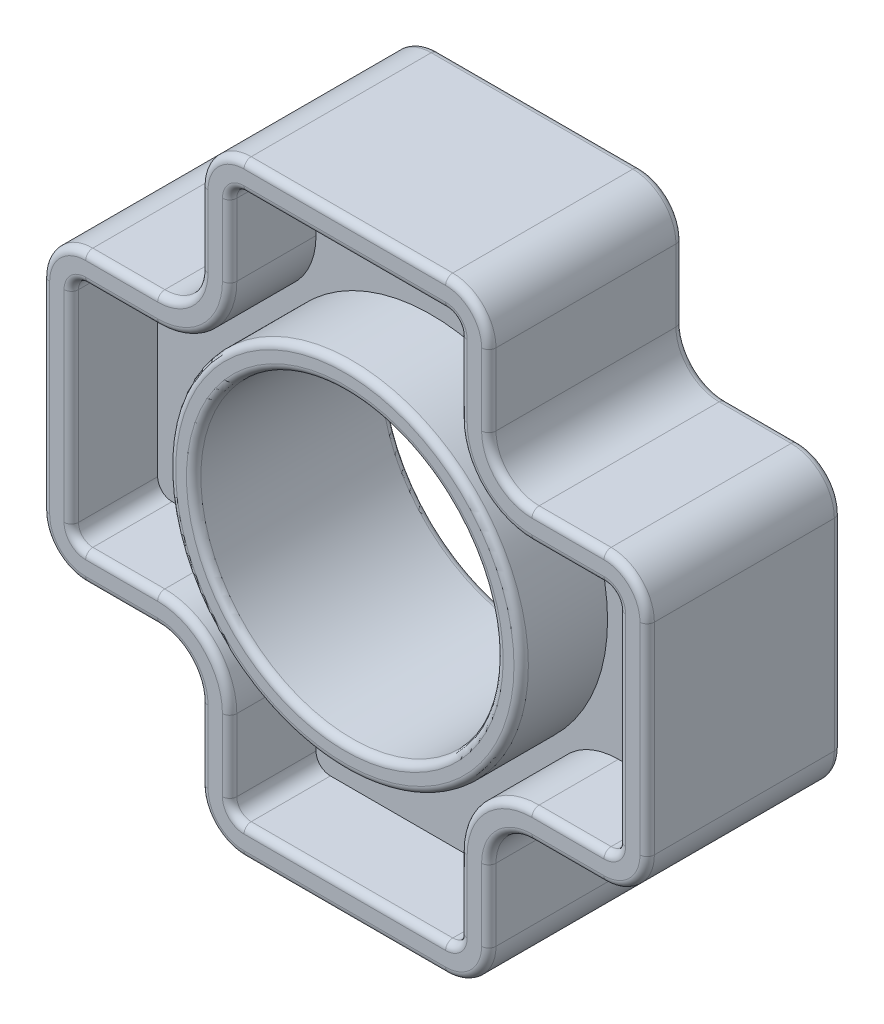
SolidWorks part; units mm, degrees
ref_plane "前基準面" through (0, 0, 0) normal (0, 0, 1) x (1, 0, 0)
ref_plane "上基準面" through (0, 0, 0) normal (0, 1, 0) x (1, 0, 0)
ref_plane "右基準面" through (0, 0, 0) normal (1, 0, 0) x (0, 0, -1)
sketch "草圖1" plane through (0, 0, 0) normal (0, 0, 1) x (1, 0, 0)
  line L0 (-10, 21) -> (-10, 10)
  line L1 (-10, 10) -> (-21, 10)
  line L2 (-21, 10) -> (-21, -10)
  line L3 (-21, -10) -> (-10, -10)
  line L4 (-10, -10) -> (-10, -21)
  line L5 (-10, -21) -> (10, -21)
  line L6 (10, -21) -> (10, -10)
  line L7 (10, -10) -> (21, -10)
  line L8 (21, -10) -> (21, 10)
  line L9 (21, 10) -> (10, 10)
  line L10 (10, 10) -> (10, 21)
  line L11 (10, 21) -> (-10, 21)
  point P2 (0, 21)
  point P13 (-21, 0)
  dimension "D1" = 20
  dimension "D2" = 11
extrude "填料-伸長1" add sketch "草圖1" along normal blind 13.5
fillet "圓角1" radius 3 12 edges at (-10, 10, 6.75) (-21, 10, 6.75) (-10, -10, 6.75) (-21, -10, 6.75) (-10, -21, 6.75) (10, -10, 6.75) (10, -21, 6.75) (21, -10, 6.75) (21, 10, 6.75) (10, 10, 6.75) (10, 21, 6.75) (-10, 21, 6.75)
sketch "草圖2" plane through (0, 0, 13.5) normal (0, 0, 1) x (1, 0, 0)
  line L24 (-13, 8) -> (-18, 8)
  line L25 (-19, 7) -> (-19, -7)
  line L26 (-18, -8) -> (-13, -8)
  line L27 (-8, -13) -> (-8, -18)
  line L28 (-7, -19) -> (7, -19)
  line L29 (8, -18) -> (8, -13)
  line L30 (13, -8) -> (18, -8)
  line L31 (19, -7) -> (19, 7)
  line L32 (18, 8) -> (13, 8)
  line L33 (8, 13) -> (8, 18)
  line L34 (7, 19) -> (-7, 19)
  line L35 (-8, 18) -> (-8, 13)
  line L36 (-13, 8) -> (-18, 8)
  line L37 (-19, 7) -> (-19, -7)
  line L38 (-18, -8) -> (-13, -8)
  line L39 (-8, -13) -> (-8, -18)
  line L40 (-7, -19) -> (7, -19)
  line L41 (8, -18) -> (8, -13)
  line L42 (13, -8) -> (18, -8)
  line L43 (19, -7) -> (19, 7)
  line L44 (18, 8) -> (13, 8)
  line L45 (8, 13) -> (8, 18)
  line L46 (7, 19) -> (-7, 19)
  line L47 (-8, 18) -> (-8, 13)
  arc A24 (-8, -13) -> (-13, -8) centre (-13, -13) ccw
  arc A25 (13, -8) -> (8, -13) centre (13, -13) ccw
  arc A26 (8, 13) -> (13, 8) centre (13, 13) ccw
  arc A27 (-13, 8) -> (-8, 13) centre (-13, 13) ccw
  arc A28 (-8, -13) -> (-13, -8) centre (-13, -13) ccw
  arc A29 (13, -8) -> (8, -13) centre (13, -13) ccw
  arc A30 (8, 13) -> (13, 8) centre (13, 13) ccw
  arc A31 (-13, 8) -> (-8, 13) centre (-13, 13) ccw
  arc A32 (-18, 8) -> (-19, 7) centre (-18, 7) ccw
  arc A33 (-18, 8) -> (-19, 7) centre (-18, 7) ccw
  arc A34 (-19, -7) -> (-18, -8) centre (-18, -7) ccw
  arc A35 (-19, -7) -> (-18, -8) centre (-18, -7) ccw
  arc A36 (-8, -18) -> (-7, -19) centre (-7, -18) ccw
  arc A37 (-8, -18) -> (-7, -19) centre (-7, -18) ccw
  arc A38 (7, -19) -> (8, -18) centre (7, -18) ccw
  arc A39 (7, -19) -> (8, -18) centre (7, -18) ccw
  arc A40 (18, -8) -> (19, -7) centre (18, -7) ccw
  arc A41 (18, -8) -> (19, -7) centre (18, -7) ccw
  arc A42 (19, 7) -> (18, 8) centre (18, 7) ccw
  arc A43 (19, 7) -> (18, 8) centre (18, 7) ccw
  arc A44 (8, 18) -> (7, 19) centre (7, 18) ccw
  arc A45 (8, 18) -> (7, 19) centre (7, 18) ccw
  arc A46 (-7, 19) -> (-8, 18) centre (-7, 18) ccw
  arc A47 (-7, 19) -> (-8, 18) centre (-7, 18) ccw
  dimension "D1" = 2
extrude "除料-伸長1" cut sketch "草圖2" against normal blind 6
sketch "草圖3" plane through (0, 0, 0) normal (0, 0, -1) x (-1, 0, 0)
  line L24 (19, -7) -> (19, 7)
  line L25 (18, 8) -> (13, 8)
  line L26 (8, 13) -> (8, 18)
  line L27 (7, 19) -> (-7, 19)
  line L28 (-8, 18) -> (-8, 13)
  line L29 (-13, 8) -> (-18, 8)
  line L30 (-19, 7) -> (-19, -7)
  line L31 (-18, -8) -> (-13, -8)
  line L32 (-8, -13) -> (-8, -18)
  line L33 (-7, -19) -> (7, -19)
  line L34 (8, -18) -> (8, -13)
  line L35 (13, -8) -> (18, -8)
  line L36 (19, -7) -> (19, 7)
  line L37 (18, 8) -> (13, 8)
  line L38 (8, 13) -> (8, 18)
  line L39 (7, 19) -> (-7, 19)
  line L40 (-8, 18) -> (-8, 13)
  line L41 (-13, 8) -> (-18, 8)
  line L42 (-19, 7) -> (-19, -7)
  line L43 (-18, -8) -> (-13, -8)
  line L44 (-8, -13) -> (-8, -18)
  line L45 (-7, -19) -> (7, -19)
  line L46 (8, -18) -> (8, -13)
  line L47 (13, -8) -> (18, -8)
  arc A24 (19, 7) -> (18, 8) centre (18, 7) ccw
  arc A25 (8, 13) -> (13, 8) centre (13, 13) ccw
  arc A26 (8, 18) -> (7, 19) centre (7, 18) ccw
  arc A27 (-7, 19) -> (-8, 18) centre (-7, 18) ccw
  arc A28 (-13, 8) -> (-8, 13) centre (-13, 13) ccw
  arc A29 (-18, 8) -> (-19, 7) centre (-18, 7) ccw
  arc A30 (-19, -7) -> (-18, -8) centre (-18, -7) ccw
  arc A31 (-8, -13) -> (-13, -8) centre (-13, -13) ccw
  arc A32 (-8, -18) -> (-7, -19) centre (-7, -18) ccw
  arc A33 (7, -19) -> (8, -18) centre (7, -18) ccw
  arc A34 (13, -8) -> (8, -13) centre (13, -13) ccw
  arc A35 (18, -8) -> (19, -7) centre (18, -7) ccw
  arc A36 (19, 7) -> (18, 8) centre (18, 7) ccw
  arc A37 (8, 13) -> (13, 8) centre (13, 13) ccw
  arc A38 (8, 18) -> (7, 19) centre (7, 18) ccw
  arc A39 (-7, 19) -> (-8, 18) centre (-7, 18) ccw
  arc A40 (-13, 8) -> (-8, 13) centre (-13, 13) ccw
  arc A41 (-18, 8) -> (-19, 7) centre (-18, 7) ccw
  arc A42 (-19, -7) -> (-18, -8) centre (-18, -7) ccw
  arc A43 (-8, -13) -> (-13, -8) centre (-13, -13) ccw
  arc A44 (-8, -18) -> (-7, -19) centre (-7, -18) ccw
  arc A45 (7, -19) -> (8, -18) centre (7, -18) ccw
  arc A46 (13, -8) -> (8, -13) centre (13, -13) ccw
  arc A47 (18, -8) -> (19, -7) centre (18, -7) ccw
  dimension "D1" = 2
extrude "除料-伸長2" cut sketch "草圖3" against normal blind 6
sketch "草圖4" plane through (0, 0, 6) normal (0, 0, -1) x (-1, 0, 0)
  circle A0 centre (0, 0) radius 12.25
  dimension "D1" = 24.5
extrude "填料-伸長3" add sketch "草圖4" along normal up to surface and the other way up to surface
sketch "草圖5" plane through (0, 0, 13.5) normal (0, 0, 1) x (1, 0, 0)
  circle A0 centre (0, 0) radius 10.5
  dimension "D1" = 21
extrude "除料-伸長3" cut sketch "草圖5" against normal up to next
fillet "圓角2" radius 0.5 100 edges at (18.7071, 7.7071, 0) (15.5, 8, 0) (9.4645, 9.4645, 0) (8, 15.5, 0) (7.7071, 18.7071, 0) (0, 19, 0) (-7.7071, 18.7071, 0) (-8, 15.5, 0) (-9.4645, 9.4645, 0) (-15.5, 8, 0) (-18.7071, 7.7071, 0) (-19, 0, 0) (-18.7071, -7.7071, 0) (-15.5, -8, 0) (-9.4645, -9.4645, 0) (-8, -15.5, 0) (-7.7071, -18.7071, 0) (0, -19, 0) (7.7071, -18.7071, 0) (8, -15.5, 0) (9.4645, -9.4645, 0) (15.5, -8, 0) (18.7071, -7.7071, 0) (20.1213, -9.1213, 0) (15.5, -10, 0) (10.8787, -10.8787, 0) (10, -15.5, 0) (9.1213, -20.1213, 0) (0, -21, 0) (-9.1213, -20.1213, 0) (-10, -15.5, 0) (-10.8787, -10.8787, 0) (-15.5, -10, 0) (-20.1213, -9.1213, 0) (-21, 0, 0) (-20.1213, 9.1213, 0) (-15.5, 10, 0) (-10.8787, 10.8787, 0) (-10, 15.5, 0) (-9.1213, 20.1213, 0) (0, 21, 0) (9.1213, 20.1213, 0) (10, 15.5, 0) (10.8787, 10.8787, 0) (15.5, 10, 0) (20.1213, 9.1213, 0) (18.7071, -7.7071, 13.5) (15.5, -8, 13.5) (9.4645, -9.4645, 13.5) (8, -15.5, 13.5) (7.7071, -18.7071, 13.5) (0, -19, 13.5) (-7.7071, -18.7071, 13.5) (-8, -15.5, 13.5) (-9.4645, -9.4645, 13.5) (-15.5, -8, 13.5) (-18.7071, -7.7071, 13.5) (-19, 0, 13.5) (-18.7071, 7.7071, 13.5) (-15.5, 8, 13.5) (-9.4645, 9.4645, 13.5) (-8, 15.5, 13.5) (-7.7071, 18.7071, 13.5) (0, 19, 13.5) (7.7071, 18.7071, 13.5) (8, 15.5, 13.5) (9.4645, 9.4645, 13.5) (15.5, 8, 13.5) (18.7071, 7.7071, 13.5) (20.1213, -9.1213, 13.5) (15.5, -10, 13.5) (10.8787, -10.8787, 13.5) (10, -15.5, 13.5) (9.1213, -20.1213, 13.5) (0, -21, 13.5) (-9.1213, -20.1213, 13.5) (-10, -15.5, 13.5) (-10.8787, -10.8787, 13.5) (-15.5, -10, 13.5) (-20.1213, -9.1213, 13.5) (-21, 0, 13.5) (-20.1213, 9.1213, 13.5) (-15.5, 10, 13.5) (-10.8787, 10.8787, 13.5) (-10, 15.5, 13.5) (-9.1213, 20.1213, 13.5) (0, 21, 13.5) (9.1213, 20.1213, 13.5) (10, 15.5, 13.5) (10.8787, 10.8787, 13.5) (15.5, 10, 13.5) (20.1213, 9.1213, 13.5) (12.25, 0, 0) (19, 0, 0) (21, 0, 0) (10.5, 0, 0) (10.5, 0, 13.5) (12.25, 0, 13.5) (19, 0, 13.5) (21, 0, 13.5)
